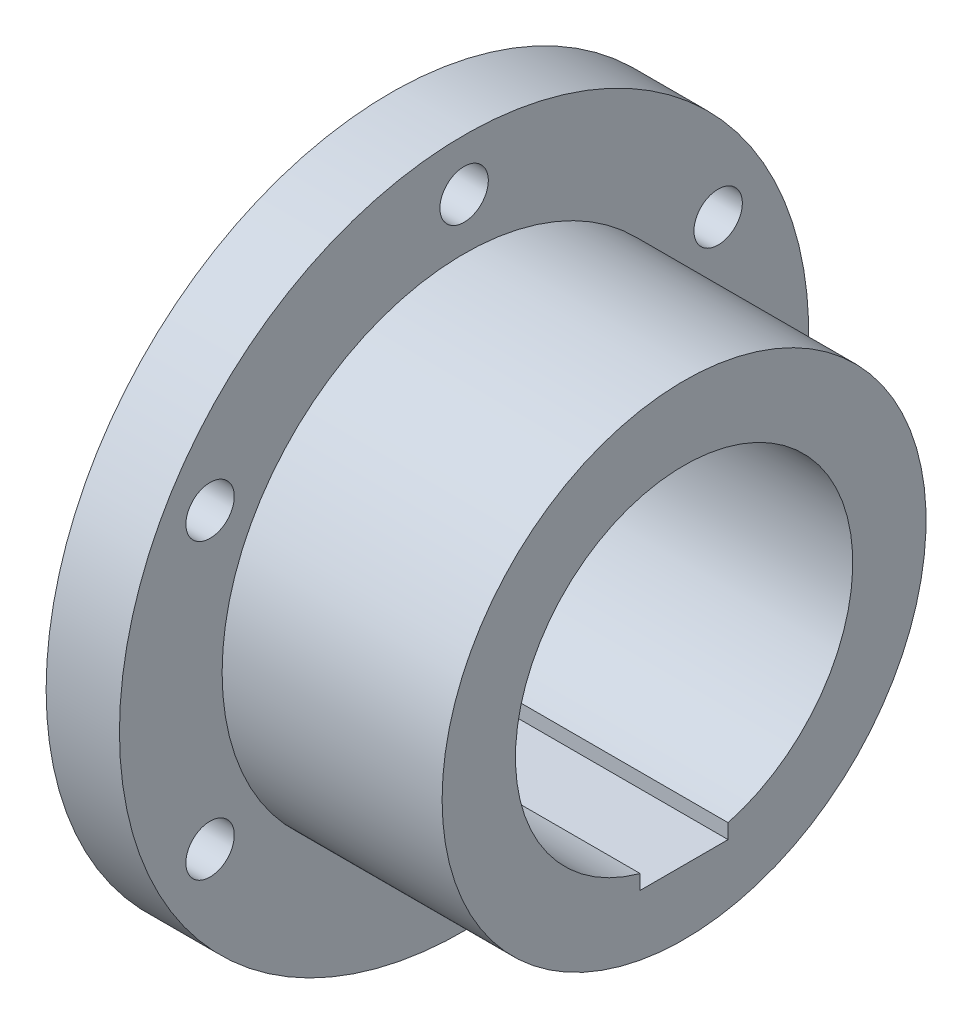
SolidWorks part; units mm, degrees
ref_plane "Front Plane" through (0, 0, 0) normal (0, 0, 1) x (1, 0, 0)
ref_plane "Top Plane" through (0, 0, 0) normal (0, 1, 0) x (1, 0, 0)
ref_plane "Right Plane" through (0, 0, 0) normal (1, 0, 0) x (0, 0, -1)
sketch "Sketch1" plane through (0, 0, 0) normal (0, 1, 0) x (1, 0, 0)
  line L0 (-31.1594, 0) -> (31.1594, 0) construction
  line L1 (0, 23) -> (46, 23)
  line L2 (46, 23) -> (46, 33)
  line L3 (46, 33) -> (16, 33)
  line L4 (16, 33) -> (16, 47)
  line L5 (16, 47) -> (6, 47)
  line L6 (6, 47) -> (6, 28)
  line L7 (6, 28) -> (0, 28)
  line L8 (0, 28) -> (0, 23)
  line L9 (0, 0) -> (0, -7.8647) construction
  point P7 (0, 0)
  dimension "D1" = 46
  dimension "D2" = 10
  dimension "D3" = 5
  dimension "D4" = 6
  dimension "D5" = 30
  dimension "D6" = 23
  dimension "D7" = 24
revolve "Revolve1" add sketch "Sketch1" angle 360 about L0
sketch "Sketch2" plane through (6, 0, 0) normal (-1, 0, 0) x (0, 0, 1)
  line L0 (0, -47) -> (0, 47) construction
  line L1 (-47, 0) -> (47, 0) construction
  circle A0 centre (0, 0) radius 28 construction
  circle A1 centre (0, 0) radius 47
  circle A2 centre (0, 0) radius 47 construction
  circle A3 centre (0, 0) radius 28 construction
  circle A4 centre (0, 40) radius 3.3
  circle A5 centre (34.641, 20) radius 3.3
  circle A6 centre (34.641, -20) radius 3.3
  circle A7 centre (0, -40) radius 3.3
  circle A8 centre (-34.641, -20) radius 3.3
  circle A9 centre (-34.641, 20) radius 3.3
  point P25 (0, 0)
  dimension "D2" = 6.6
  dimension "D3" = 40
  dimension "D4" = 47
  dimension "D1" = 0
  dimension "D5" = 6
extrude "Cut-Extrude1" cut sketch "Sketch2" against normal through all
sketch "Sketch3" plane through (0, 0, 0) normal (-1, 0, 0) x (0, 0, 1)
  line L0 (0, 19) -> (0, -19) construction
  line L1 (-23, 0) -> (23, 0) construction
  line L2 (-6, -24.2036) -> (6, -24.2036)
  line L6 (-6, -24.2036) -> (-6, -22.2036)
  line L7 (6, -24.2036) -> (6, -22.2036)
  line L8 (-6, -22.2036) -> (6, -22.2036)
  circle A0 centre (0, 0) radius 23 construction
  circle A1 centre (0, 0) radius 28 construction
  circle A2 centre (0, 0) radius 23 construction
  circle A3 centre (0, 0) radius 28 construction
  point P1 (0, -24.2036)
  dimension "D1" = 2
  dimension "D2" = 12
  dimension "D3" = 2
extrude "Cut-Extrude2" cut sketch "Sketch3" against normal through all
